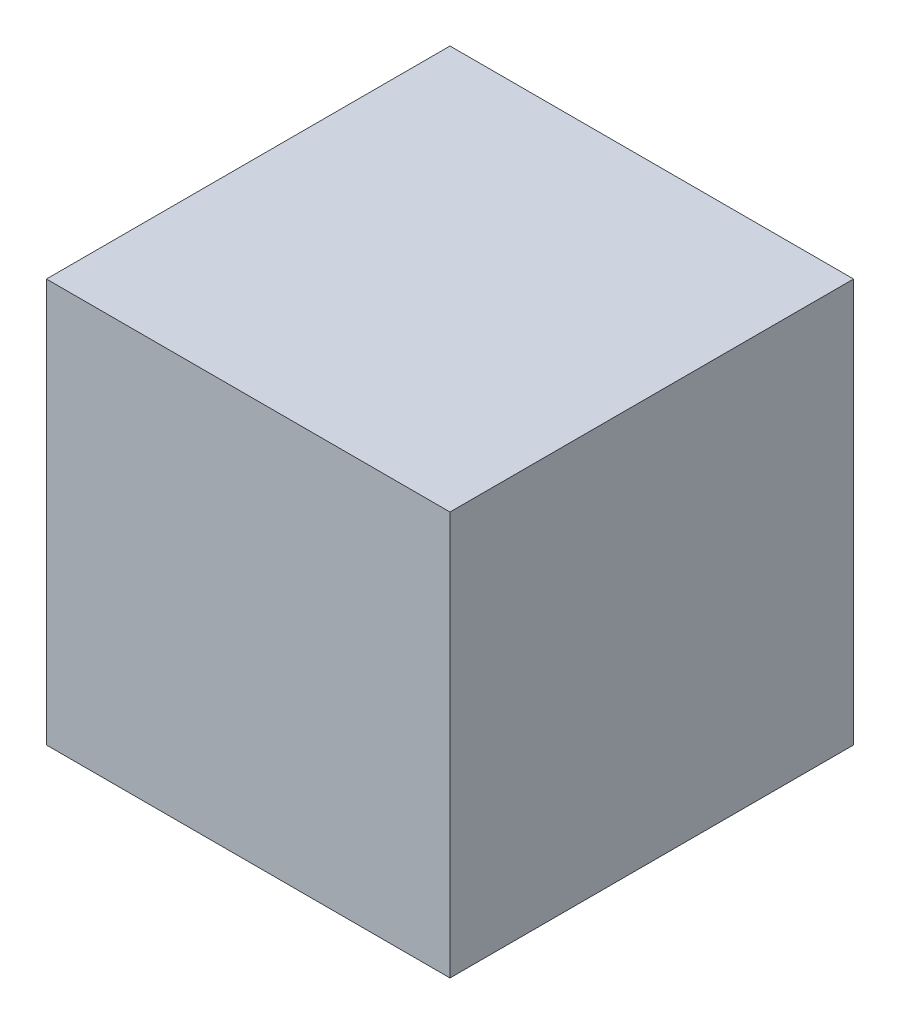
SolidWorks part; units mm, degrees
material "Oak"
ref_plane "Front Plane" through (0, 0, 0) normal (0, 0, 1) x (1, 0, 0)
ref_plane "Top Plane" through (0, 0, 0) normal (0, 1, 0) x (1, 0, 0)
ref_plane "Right Plane" through (0, 0, 0) normal (1, 0, 0) x (0, 0, -1)
sketch "Sketch1" plane through (0, 0, 0) normal (0, 0, 1) x (1, 0, 0)
  line L1 (0, 0) -> (127, 0)
  line L2 (0, 0) -> (0, 127)
  line L3 (0, 127) -> (127, 127)
  line L4 (127, 0) -> (127, 127)
  dimension "D1" = 127
extrude "Boss-Extrude1" add sketch "Sketch1" along normal blind 127
